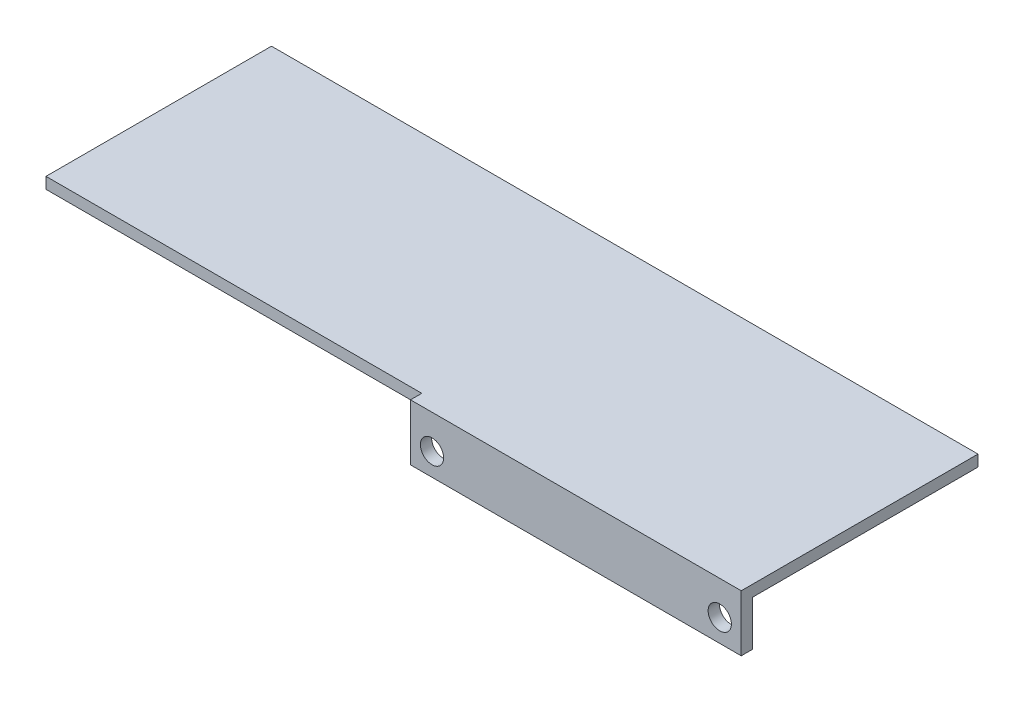
SolidWorks part; units mm, degrees
material "PTFE(普通)"
ref_plane "前视基准面" through (0, 0, 0) normal (0, 0, 1) x (1, 0, 0)
ref_plane "上视基准面" through (0, 0, 0) normal (0, 1, 0) x (1, 0, 0)
ref_plane "右视基准面" through (0, 0, 0) normal (1, 0, 0) x (0, 0, -1)
other "Configuration Table"
sketch "草图1" plane through (0, 0, 0) normal (0, 0, 1) x (1, 0, 0)
  line L1 (22, -3) -> (-22, -3)
  line L2 (22, -3) -> (22, 3)
  line L3 (22, 3) -> (-22, 3)
  line L4 (-22, -3) -> (-22, 3)
  line L5 (22, -3) -> (-22, 3) construction
  line L6 (22, 3) -> (-22, -3) construction
  circle A0 centre (-19.1442, 0) radius 1.55
  circle A1 centre (19.1442, 0) radius 1.55
  point P0 (0, 0)
  point P6 (-19.1442, 0)
  point P7 (19.1442, 0)
  dimension "D3" = 3.1
  dimension "D4" = 3.1
  dimension "D1" = 19.1442
  dimension "D2" = 19.1442
  dimension "D5" = 22
  dimension "D6" = 3
extrude "凸台-拉伸1" add sketch "草图1" along normal blind 1.5
sketch "草图2" plane through (0, 3, 0) normal (0, 1, 0) x (1, 0, 0)
  line L1 (-22, 0) -> (22, 0)
  line L2 (-22, 0) -> (-22, -1.5)
  line L3 (-22, -1.5) -> (22, -1.5)
  line L4 (22, 0) -> (22, -1.5)
extrude "凸台-拉伸2" add sketch "草图2" along normal blind 1.5
sketch "草图3" plane through (0, 0, 1.5) normal (0, 0, 1) x (1, 0, 0)
  line L0 (22, -3) -> (22, 4.5) construction
  line L1 (-22, 4.5) -> (22, 4.5)
  line L2 (-22, 4.5) -> (-22, 3)
  line L3 (-22, 3) -> (22, 3)
  line L4 (22, 4.5) -> (22, 3)
  dimension "D1" = 1.5
sketch "草图4" plane through (0, 0, 0) normal (0, 0, -1) x (-1, 0, 0)
  line L1 (-22, 4.5) -> (22, 4.5)
  line L2 (-22, 4.5) -> (-22, 3)
  line L3 (-22, 3) -> (22, 3)
  line L4 (22, 4.5) -> (22, 3)
extrude "凸台-拉伸3" add sketch "草图4" along normal blind 30
sketch "草图6" plane through (-22, 0, 0) normal (-1, 0, 0) x (0, 0, 1)
  line L1 (-30, 4.5) -> (0, 4.5)
  line L2 (-30, 4.5) -> (-30, 3)
  line L3 (-30, 3) -> (0, 3)
  line L4 (0, 4.5) -> (0, 3)
extrude "凸台-拉伸4" add sketch "草图6" along normal blind 50
